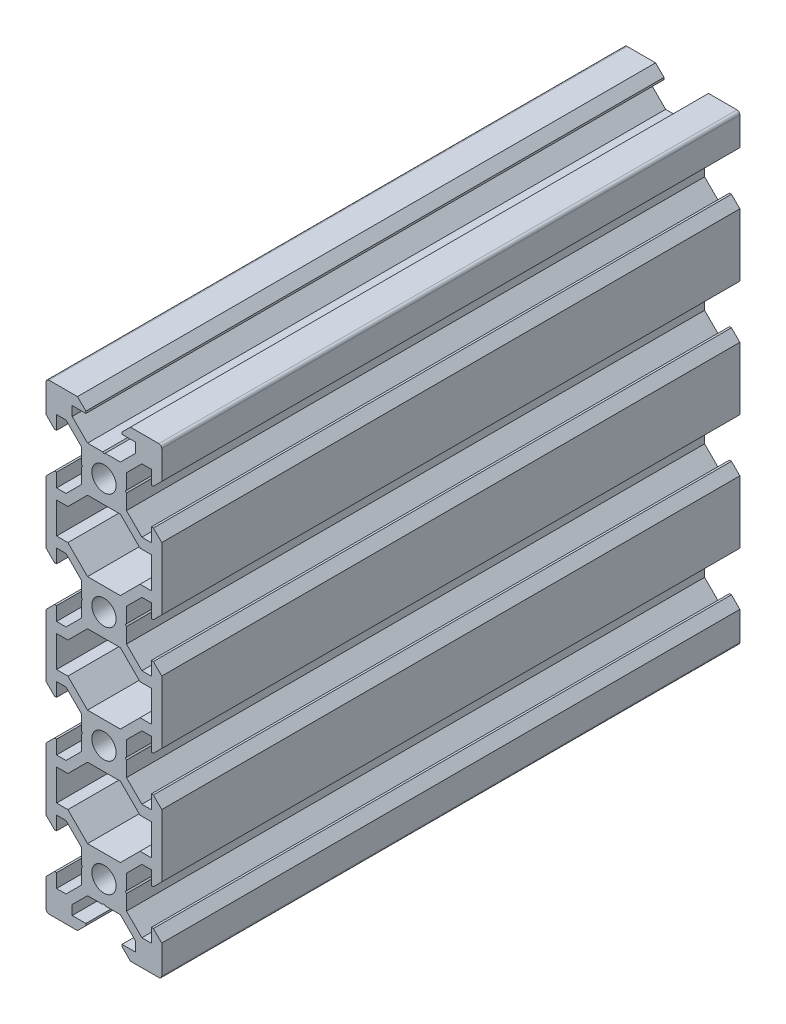
SolidWorks part; units mm, degrees
material "6061-T6 (SS)"
ref_plane "Front Plane" through (0, 0, 0) normal (0, 0, 1) x (1, 0, 0)
ref_plane "Top Plane" through (0, 0, 0) normal (0, 1, 0) x (1, 0, 0)
ref_plane "Right Plane" through (0, 0, 0) normal (1, 0, 0) x (0, 0, -1)
sketch "Sketch1" plane through (0, 0, 0) normal (0, 0, 1) x (1, 0, 0)
  line L0 (0, 0) -> (10, 0) construction
  line L1 (9.5, -40) -> (-9.5, -40)
  line L2 (10, -39.5) -> (10, 39.5)
  line L3 (9.5, 40) -> (-9.5, 40)
  line L4 (-10, -39.5) -> (-10, 39.5)
  line L5 (10, -40) -> (-10, 40) construction
  line L6 (10, 40) -> (-10, -40) construction
  circle A0 centre (0, 30) radius 2.1
  circle A1 centre (0, 10) radius 2.1
  circle A2 centre (0, -10) radius 2.1
  circle A3 centre (0, -30) radius 2.1
  arc A4 (-9.5, -40) -> (-10, -39.5) centre (-9.5, -39.5) cw
  arc A5 (9.5, -40) -> (10, -39.5) centre (9.5, -39.5) ccw
  arc A6 (10, 39.5) -> (9.5, 40) centre (9.5, 39.5) ccw
  arc A7 (-9.5, 40) -> (-10, 39.5) centre (-9.5, 39.5) ccw
  point P0 (0, 0)
  line B0 (0, 30) -> (0, 40) construction
  line B1 (0, 33.69) -> (-0.21, 33.9)
  line B2 (-0.21, 33.9) -> (-2.8393, 33.9)
  line B3 (-2.8393, 33.9) -> (-5.5, 36.5607)
  line B4 (-5.5, 36.5607) -> (-5.5, 38.2)
  line B5 (-5.5, 38.2) -> (-3.125, 38.2)
  line B6 (-3.125, 38.2) -> (-3.125, 38.545)
  line B7 (-3.125, 38.545) -> (-4.58, 40)
  line B8 (-4.58, 40) -> (4.58, 40)
  line B9 (0, 30) -> (-5.9132, 35.9132) construction
  line B10 (3.125, 38.545) -> (4.58, 40)
  line B11 (3.125, 38.2) -> (3.125, 38.545)
  line B12 (5.5, 38.2) -> (3.125, 38.2)
  line B13 (5.5, 36.5607) -> (5.5, 38.2)
  line B14 (2.8393, 33.9) -> (5.5, 36.5607)
  line B15 (0.21, 33.9) -> (2.8393, 33.9)
  line B16 (0, 33.69) -> (0.21, 33.9)
  line B17 (0, 30) -> (-10, 30) construction
  line B18 (-3.69, 30) -> (-3.9, 29.79)
  line B19 (-3.9, 29.79) -> (-3.9, 27.1607)
  line B20 (-3.9, 27.1607) -> (-6.5607, 24.5)
  line B21 (-6.5607, 24.5) -> (-8.2, 24.5)
  line B22 (-8.2, 24.5) -> (-8.2, 26.875)
  line B23 (-8.2, 26.875) -> (-8.545, 26.875)
  line B24 (-8.545, 26.875) -> (-10, 25.42)
  line B25 (-10, 25.42) -> (-10, 34.58)
  line B26 (0, 30) -> (-5.9132, 24.0868) construction
  line B27 (-8.545, 33.125) -> (-10, 34.58)
  line B28 (-8.2, 33.125) -> (-8.545, 33.125)
  line B29 (-8.2, 35.5) -> (-8.2, 33.125)
  line B30 (-6.5607, 35.5) -> (-8.2, 35.5)
  line B31 (-3.9, 32.8393) -> (-6.5607, 35.5)
  line B32 (-3.9, 30.21) -> (-3.9, 32.8393)
  line B33 (-3.69, 30) -> (-3.9, 30.21)
  line B34 (0, 10) -> (-10, 10) construction
  line B35 (-3.69, 10) -> (-3.9, 9.79)
  line B36 (-3.9, 9.79) -> (-3.9, 7.1607)
  line B37 (-3.9, 7.1607) -> (-6.5607, 4.5)
  line B38 (-6.5607, 4.5) -> (-8.2, 4.5)
  line B39 (-8.2, 4.5) -> (-8.2, 6.875)
  line B40 (-8.2, 6.875) -> (-8.545, 6.875)
  line B41 (-8.545, 6.875) -> (-10, 5.42)
  line B42 (-10, 5.42) -> (-10, 14.58)
  line B43 (0, 10) -> (-5.9132, 4.0868) construction
  line B44 (-8.545, 13.125) -> (-10, 14.58)
  line B45 (-8.2, 13.125) -> (-8.545, 13.125)
  line B46 (-8.2, 15.5) -> (-8.2, 13.125)
  line B47 (-6.5607, 15.5) -> (-8.2, 15.5)
  line B48 (-3.9, 12.8393) -> (-6.5607, 15.5)
  line B49 (-3.9, 10.21) -> (-3.9, 12.8393)
  line B50 (-3.69, 10) -> (-3.9, 10.21)
  line B51 (0, -10) -> (-10, -10) construction
  line B52 (-3.69, -10) -> (-3.9, -10.21)
  line B53 (-3.9, -10.21) -> (-3.9, -12.8393)
  line B54 (-3.9, -12.8393) -> (-6.5607, -15.5)
  line B55 (-6.5607, -15.5) -> (-8.2, -15.5)
  line B56 (-8.2, -15.5) -> (-8.2, -13.125)
  line B57 (-8.2, -13.125) -> (-8.545, -13.125)
  line B58 (-8.545, -13.125) -> (-10, -14.58)
  line B59 (-10, -14.58) -> (-10, -5.42)
  line B60 (0, -10) -> (-5.9132, -15.9132) construction
  line B61 (-8.545, -6.875) -> (-10, -5.42)
  line B62 (-8.2, -6.875) -> (-8.545, -6.875)
  line B63 (-8.2, -4.5) -> (-8.2, -6.875)
  line B64 (-6.5607, -4.5) -> (-8.2, -4.5)
  line B65 (-3.9, -7.1607) -> (-6.5607, -4.5)
  line B66 (-3.9, -9.79) -> (-3.9, -7.1607)
  line B67 (-3.69, -10) -> (-3.9, -9.79)
  line B68 (0, -30) -> (-10, -30) construction
  line B69 (-3.69, -30) -> (-3.9, -30.21)
  line B70 (-3.9, -30.21) -> (-3.9, -32.8393)
  line B71 (-3.9, -32.8393) -> (-6.5607, -35.5)
  line B72 (-6.5607, -35.5) -> (-8.2, -35.5)
  line B73 (-8.2, -35.5) -> (-8.2, -33.125)
  line B74 (-8.2, -33.125) -> (-8.545, -33.125)
  line B75 (-8.545, -33.125) -> (-10, -34.58)
  line B76 (-10, -34.58) -> (-10, -25.42)
  line B77 (0, -30) -> (-5.9132, -35.9132) construction
  line B78 (-8.545, -26.875) -> (-10, -25.42)
  line B79 (-8.2, -26.875) -> (-8.545, -26.875)
  line B80 (-8.2, -24.5) -> (-8.2, -26.875)
  line B81 (-6.5607, -24.5) -> (-8.2, -24.5)
  line B82 (-3.9, -27.1607) -> (-6.5607, -24.5)
  line B83 (-3.9, -29.79) -> (-3.9, -27.1607)
  line B84 (-3.69, -30) -> (-3.9, -29.79)
  line B85 (0, -30) -> (0, -40) construction
  line B86 (0, -33.69) -> (0.21, -33.9)
  line B87 (0.21, -33.9) -> (2.8393, -33.9)
  line B88 (2.8393, -33.9) -> (5.5, -36.5607)
  line B89 (5.5, -36.5607) -> (5.5, -38.2)
  line B90 (5.5, -38.2) -> (3.125, -38.2)
  line B91 (3.125, -38.2) -> (3.125, -38.545)
  line B92 (3.125, -38.545) -> (4.58, -40)
  line B93 (4.58, -40) -> (-4.58, -40)
  line B94 (0, -30) -> (5.9132, -35.9132) construction
  line B95 (-3.125, -38.545) -> (-4.58, -40)
  line B96 (-3.125, -38.2) -> (-3.125, -38.545)
  line B97 (-5.5, -38.2) -> (-3.125, -38.2)
  line B98 (-5.5, -36.5607) -> (-5.5, -38.2)
  line B99 (-2.8393, -33.9) -> (-5.5, -36.5607)
  line B100 (-0.21, -33.9) -> (-2.8393, -33.9)
  line B101 (0, -33.69) -> (-0.21, -33.9)
  line B102 (0, -30) -> (10, -30) construction
  line B103 (3.69, -30) -> (3.9, -29.79)
  line B104 (3.9, -29.79) -> (3.9, -27.1607)
  line B105 (3.9, -27.1607) -> (6.5607, -24.5)
  line B106 (6.5607, -24.5) -> (8.2, -24.5)
  line B107 (8.2, -24.5) -> (8.2, -26.875)
  line B108 (8.2, -26.875) -> (8.545, -26.875)
  line B109 (8.545, -26.875) -> (10, -25.42)
  line B110 (10, -25.42) -> (10, -34.58)
  line B111 (0, -30) -> (5.9132, -24.0868) construction
  line B112 (8.545, -33.125) -> (10, -34.58)
  line B113 (8.2, -33.125) -> (8.545, -33.125)
  line B114 (8.2, -35.5) -> (8.2, -33.125)
  line B115 (6.5607, -35.5) -> (8.2, -35.5)
  line B116 (3.9, -32.8393) -> (6.5607, -35.5)
  line B117 (3.9, -30.21) -> (3.9, -32.8393)
  line B118 (3.69, -30) -> (3.9, -30.21)
  line B119 (0, -10) -> (10, -10) construction
  line B120 (3.69, -10) -> (3.9, -9.79)
  line B121 (3.9, -9.79) -> (3.9, -7.1607)
  line B122 (3.9, -7.1607) -> (6.5607, -4.5)
  line B123 (6.5607, -4.5) -> (8.2, -4.5)
  line B124 (8.2, -4.5) -> (8.2, -6.875)
  line B125 (8.2, -6.875) -> (8.545, -6.875)
  line B126 (8.545, -6.875) -> (10, -5.42)
  line B127 (10, -5.42) -> (10, -14.58)
  line B128 (0, -10) -> (5.9132, -4.0868) construction
  line B129 (8.545, -13.125) -> (10, -14.58)
  line B130 (8.2, -13.125) -> (8.545, -13.125)
  line B131 (8.2, -15.5) -> (8.2, -13.125)
  line B132 (6.5607, -15.5) -> (8.2, -15.5)
  line B133 (3.9, -12.8393) -> (6.5607, -15.5)
  line B134 (3.9, -10.21) -> (3.9, -12.8393)
  line B135 (3.69, -10) -> (3.9, -10.21)
  line B136 (0, 10) -> (10, 10) construction
  line B137 (3.69, 10) -> (3.9, 10.21)
  line B138 (3.9, 10.21) -> (3.9, 12.8393)
  line B139 (3.9, 12.8393) -> (6.5607, 15.5)
  line B140 (6.5607, 15.5) -> (8.2, 15.5)
  line B141 (8.2, 15.5) -> (8.2, 13.125)
  line B142 (8.2, 13.125) -> (8.545, 13.125)
  line B143 (8.545, 13.125) -> (10, 14.58)
  line B144 (10, 14.58) -> (10, 5.42)
  line B145 (0, 10) -> (5.9132, 15.9132) construction
  line B146 (8.545, 6.875) -> (10, 5.42)
  line B147 (8.2, 6.875) -> (8.545, 6.875)
  line B148 (8.2, 4.5) -> (8.2, 6.875)
  line B149 (6.5607, 4.5) -> (8.2, 4.5)
  line B150 (3.9, 7.1607) -> (6.5607, 4.5)
  line B151 (3.9, 9.79) -> (3.9, 7.1607)
  line B152 (3.69, 10) -> (3.9, 9.79)
  line B153 (0, 30) -> (10, 30) construction
  line B154 (3.69, 30) -> (3.9, 30.21)
  line B155 (3.9, 30.21) -> (3.9, 32.8393)
  line B156 (3.9, 32.8393) -> (6.5607, 35.5)
  line B157 (6.5607, 35.5) -> (8.2, 35.5)
  line B158 (8.2, 35.5) -> (8.2, 33.125)
  line B159 (8.2, 33.125) -> (8.545, 33.125)
  line B160 (8.545, 33.125) -> (10, 34.58)
  line B161 (10, 34.58) -> (10, 25.42)
  line B162 (0, 30) -> (5.9132, 35.9132) construction
  line B163 (8.545, 26.875) -> (10, 25.42)
  line B164 (8.2, 26.875) -> (8.545, 26.875)
  line B165 (8.2, 24.5) -> (8.2, 26.875)
  line B166 (6.5607, 24.5) -> (8.2, 24.5)
  line B167 (3.9, 27.1607) -> (6.5607, 24.5)
  line B168 (3.9, 29.79) -> (3.9, 27.1607)
  line B169 (3.69, 30) -> (3.9, 29.79)
  line B170 (-8.2, 17.3) -> (-8.2, 22.7)
  line B171 (-8.2, 22.7) -> (-6.2393, 22.7)
  line B172 (-6.2393, 22.7) -> (-2.8393, 26.1)
  line B173 (-2.8393, 26.1) -> (2.8393, 26.1)
  line B174 (0, 26.1) -> (0, 20) construction
  line B175 (0, 20) -> (-8.2, 20) construction
  line B176 (6.2393, 22.7) -> (2.8393, 26.1)
  line B177 (8.2, 22.7) -> (6.2393, 22.7)
  line B178 (8.2, 17.3) -> (8.2, 22.7)
  line B179 (8.2, 17.3) -> (6.2393, 17.3)
  line B180 (6.2393, 17.3) -> (2.8393, 13.9)
  line B181 (-2.8393, 13.9) -> (2.8393, 13.9)
  line B182 (-6.2393, 17.3) -> (-2.8393, 13.9)
  line B183 (-8.2, 17.3) -> (-6.2393, 17.3)
  line B184 (0, 26.1) -> (0, 30) construction
  line B185 (0, 30) -> (-5.0927, 24.9073) construction
  line B186 (-8.2, -2.7) -> (-8.2, 2.7)
  line B187 (-8.2, 2.7) -> (-6.2393, 2.7)
  line B188 (-6.2393, 2.7) -> (-2.8393, 6.1)
  line B189 (-2.8393, 6.1) -> (2.8393, 6.1)
  line B190 (0, 6.1) -> (0, 0) construction
  line B191 (0, 0) -> (-8.2, 0) construction
  line B192 (6.2393, 2.7) -> (2.8393, 6.1)
  line B193 (8.2, 2.7) -> (6.2393, 2.7)
  line B194 (8.2, -2.7) -> (8.2, 2.7)
  line B195 (8.2, -2.7) -> (6.2393, -2.7)
  line B196 (6.2393, -2.7) -> (2.8393, -6.1)
  line B197 (-2.8393, -6.1) -> (2.8393, -6.1)
  line B198 (-6.2393, -2.7) -> (-2.8393, -6.1)
  line B199 (-8.2, -2.7) -> (-6.2393, -2.7)
  line B200 (0, 6.1) -> (0, 10) construction
  line B201 (0, 10) -> (-5.0927, 4.9073) construction
  line B202 (-8.2, -22.7) -> (-8.2, -17.3)
  line B203 (-8.2, -17.3) -> (-6.2393, -17.3)
  line B204 (-6.2393, -17.3) -> (-2.8393, -13.9)
  line B205 (-2.8393, -13.9) -> (2.8393, -13.9)
  line B206 (0, -13.9) -> (0, -20) construction
  line B207 (0, -20) -> (-8.2, -20) construction
  line B208 (6.2393, -17.3) -> (2.8393, -13.9)
  line B209 (8.2, -17.3) -> (6.2393, -17.3)
  line B210 (8.2, -22.7) -> (8.2, -17.3)
  line B211 (8.2, -22.7) -> (6.2393, -22.7)
  line B212 (6.2393, -22.7) -> (2.8393, -26.1)
  line B213 (-2.8393, -26.1) -> (2.8393, -26.1)
  line B214 (-6.2393, -22.7) -> (-2.8393, -26.1)
  line B215 (-8.2, -22.7) -> (-6.2393, -22.7)
  line B216 (0, -13.9) -> (0, -10) construction
  line B217 (0, -10) -> (-5.0927, -15.0927) construction
  dimension "D5" = 4.2
  dimension "D6" = 0.5
  dimension "D1" = 20
  dimension "D2" = 80
  dimension "D3" = 20
  dimension "D4" = 20
sketch_block_instance "V Slot 1-4"
sketch_block "V Slot 1" parameters "D1"=10, "D2"=11, "D3"=4.3, "D4"=1.8, "D5"=0.21, "D6"=45, "D7"=9.16, "D8"=1.5, "D9"=6.25
sketch_block_instance "V Slot 1-5"
sketch_block_instance "V Slot 1-6"
sketch_block_instance "V Slot 1-7"
sketch_block_instance "V Slot 1-8"
sketch_block_instance "V Slot 1-9"
sketch_block_instance "V Slot 1-10"
sketch_block_instance "V Slot 1-11"
sketch_block_instance "V Slot 1-12"
sketch_block_instance "V Slot 1-13"
sketch_block_instance "Center Cutout 1-1"
sketch_block "Center Cutout 1" parameters "D1"=5.4, "D2"=12.2, "D3"=8.2, "D4"=45, "D5"=10, "D6"=1.5
sketch_block_instance "Center Cutout 1-2"
sketch_block_instance "Center Cutout 1-3"
extrude "Boss-Extrude1" add sketch "Sketch1" along normal blind 100 contours B169 B154 B155 B156 B157 B158 B159 B160 L2 A6 L3 B10 B11 B12 B13 B14 B15 B16 B1 B2 B3 B4 B5 B6 B7 A7 L4 B27 B28 B29 B30 B31 B32 B33 B18 B19 B20 B21 B22 B23 B24 B44 B45 B46 B47 B48 B49 B50 B35
